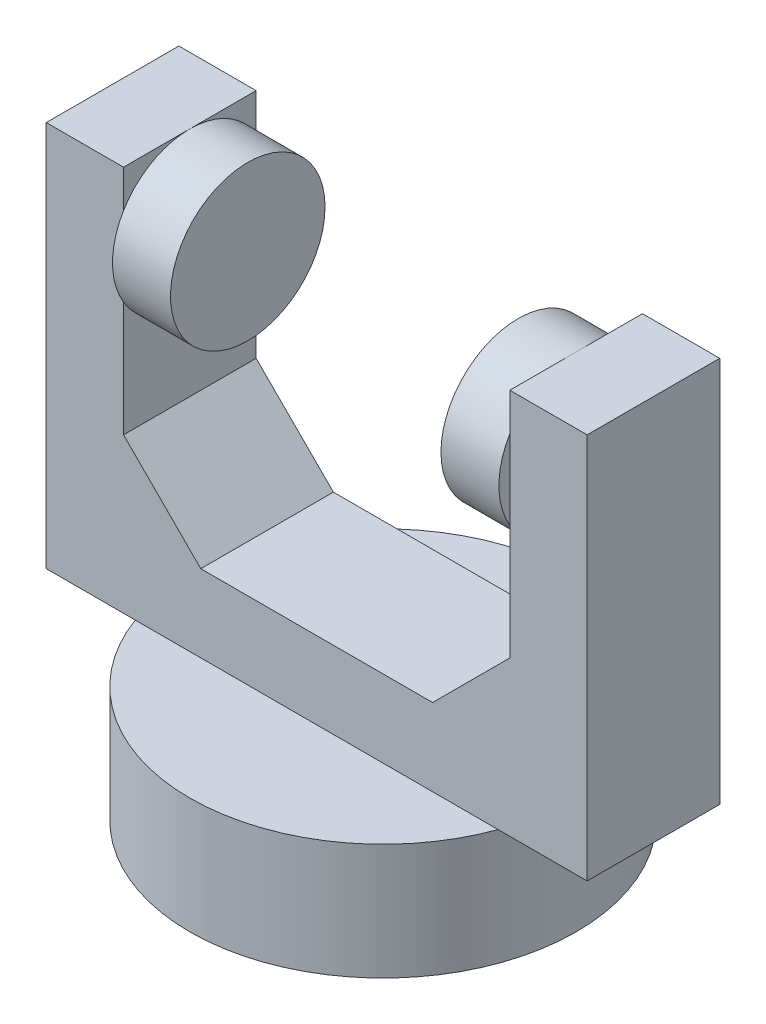
SolidWorks part; units mm, degrees
ref_plane "Front Plane" through (0, 0, 0) normal (0, 0, 1) x (1, 0, 0)
ref_plane "Top Plane" through (0, 0, 0) normal (0, 1, 0) x (1, 0, 0)
ref_plane "Right Plane" through (0, 0, 0) normal (1, 0, 0) x (0, 0, -1)
sketch "Sketch1" plane through (0, 0, 0) normal (0, 1, 0) x (1, 0, 0)
  circle A0 centre (0, 0) radius 12.5
  dimension "D1" = 25
extrude "Boss-Extrude1" add sketch "Sketch1" along normal blind 7.5
sketch "Sketch2" plane through (0, 7.5, 0) normal (0, 1, 0) x (1, 0, 0)
  line L1 (-17.5, 4.2904) -> (17.5, 4.2904)
  line L2 (-17.5, 4.2904) -> (-17.5, -4.2904)
  line L3 (-17.5, -4.2904) -> (17.5, -4.2904)
  line L4 (17.5, 4.2904) -> (17.5, -4.2904)
  point P4 (17.5, 0)
  point P6 (0, 4.2904)
  dimension "D1" = 35
  dimension "D3" = 8.5808
extrude "Boss-Extrude2" add sketch "Sketch2" along normal blind 25
sketch "Sketch3" plane through (0, 32.5, 0) normal (0, 1, 0) x (1, 0, 0)
  line L0 (17.5, 4.2904) -> (-17.5, 4.2904) construction
  line L1 (-12.5, 4.2904) -> (12.5, 4.2904)
  line L2 (-12.5, 4.2904) -> (-12.5, -4.2904)
  line L3 (-12.5, -4.2904) -> (12.5, -4.2904)
  line L4 (12.5, 4.2904) -> (12.5, -4.2904)
  line L5 (-17.5, -4.2904) -> (17.5, -4.2904) construction
  line L6 (17.5, -4.2904) -> (17.5, 4.2904) construction
  line L7 (-17.5, 4.2904) -> (-17.5, -4.2904) construction
  dimension "D1" = 5
  dimension "D2" = 5
extrude "Cut-Extrude1" cut sketch "Sketch3" against normal blind 20
sketch "Sketch4" plane through (-12.5, 0, 0) normal (1, 0, 0) x (0, 0, -1)
  line L0 (4.2904, 12.5) -> (-4.2904, 12.5) construction
  line L1 (4.2904, 32.5) -> (-4.2904, 32.5) construction
  circle A0 centre (0, 27.5) radius 5
  point P8 (0, 32.5)
  dimension "D1" = 10
  dimension "D2" = 15
extrude "Boss-Extrude3" add sketch "Sketch4" along normal blind 3.75
sketch "Sketch5" plane through (12.5, 0, 0) normal (-1, 0, 0) x (0, 0, 1)
  circle A0 centre (0, 27.5) radius 5
  circle A1 centre (0, 27.5) radius 5 construction
  dimension "D1" = 10
extrude "Boss-Extrude4" add sketch "Sketch5" along normal blind 3.75
chamfer "Chamfer1" distance 5 angle 45 1 edges at (-12.5, 12.5, 0)
chamfer "Chamfer2" distance 5 angle 45 1 edges at (12.5, 12.5, 0)
